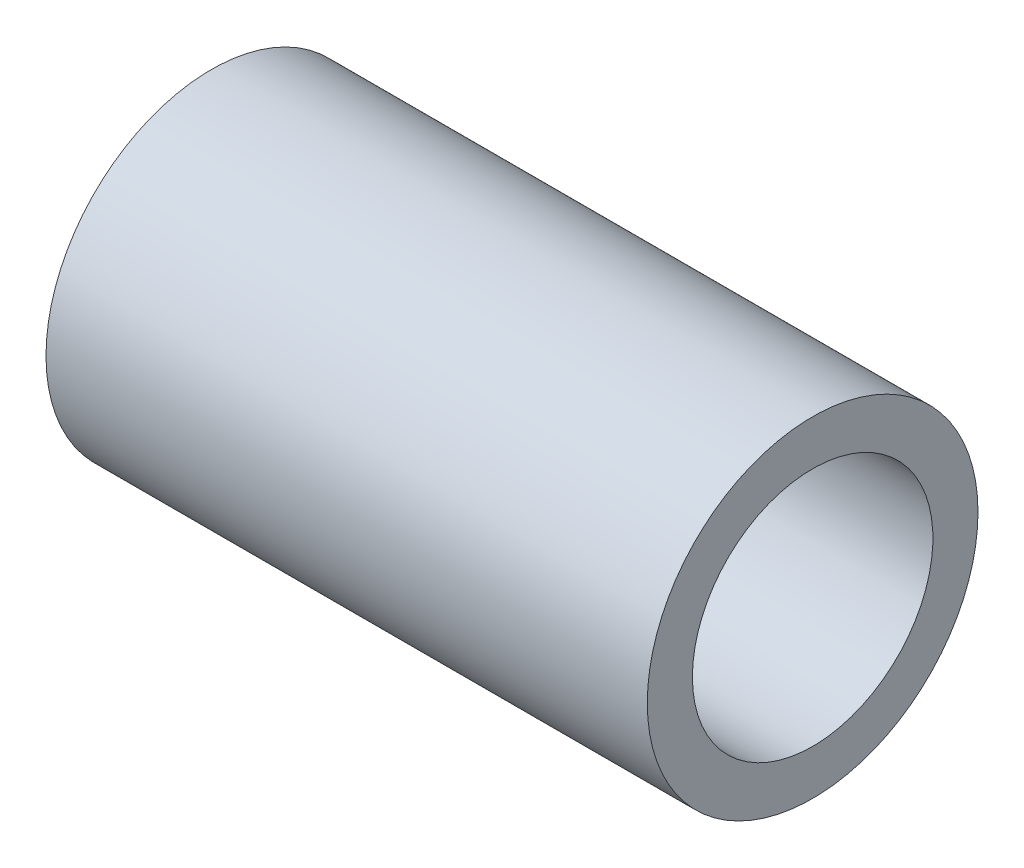
SolidWorks part; units mm, degrees
ref_plane "Front" through (0, 0, 0) normal (0, 0, 1) x (1, 0, 0)
ref_plane "Top" through (0, 0, 0) normal (0, 1, 0) x (1, 0, 0)
ref_plane "Right" through (0, 0, 0) normal (1, 0, 0) x (0, 0, -1)
sketch "Sketch2" plane through (0, 0, 0) normal (0, 0, 1) x (1, 0, 0)
  line L21 (0, 0) -> (26.8504, 0) construction
  line L23 (2, 4) -> (22, 4)
  line L24 (2, 4) -> (2, 5.5)
  line L25 (2, 5.5) -> (22, 5.5)
  line L26 (22, 4) -> (22, 5.5)
  dimension "D14" = 4
  dimension "D15" = 5.5
  dimension "D2" = 2
  dimension "D16" = 20
revolve "Revolve1" add sketch "Sketch2" angle 360 about L21
equation "\"rod_length_xaxis\"= 300.7"
equation "\"linear-xbar-dia\"= 8mm ' Diameter of the metal slide bar used on the X Axis"
